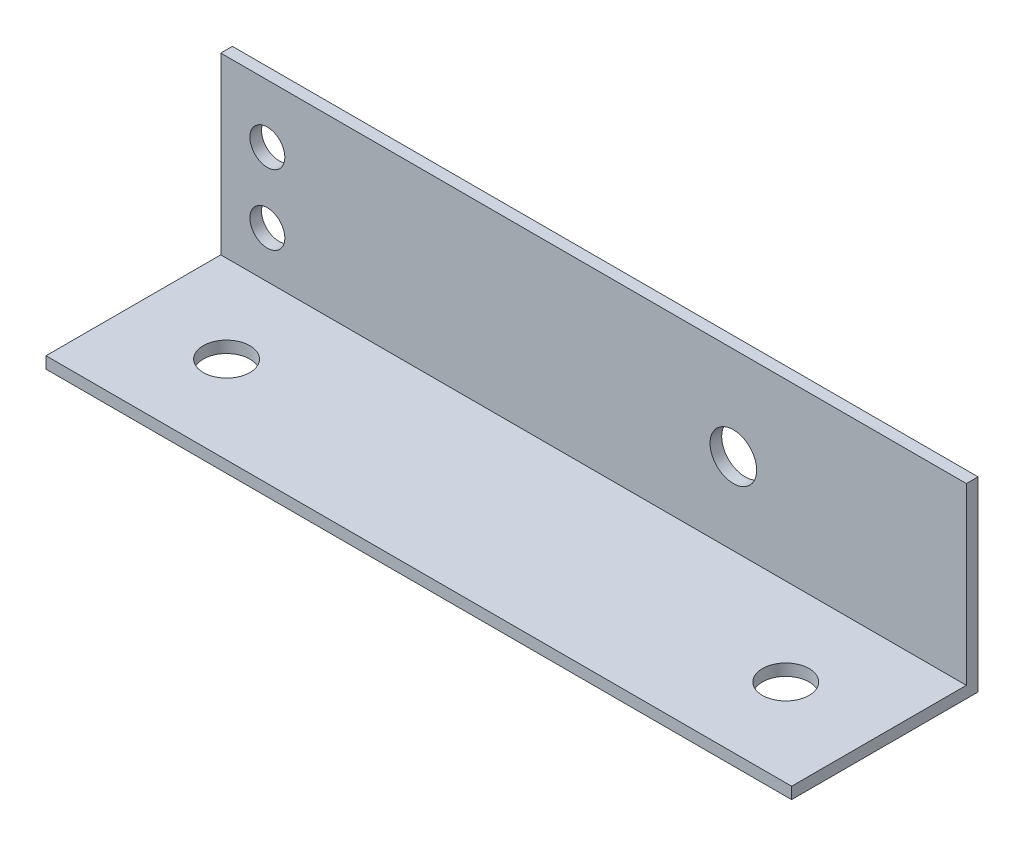
SolidWorks part; units mm, degrees
ref_plane "Front Plane" through (0, 0, 0) normal (0, 0, 1) x (1, 0, 0)
ref_plane "Top Plane" through (0, 0, 0) normal (0, 1, 0) x (1, 0, 0)
ref_plane "Right Plane" through (0, 0, 0) normal (1, 0, 0) x (0, 0, -1)
sketch "Sketch1" plane through (0, 0, 0) normal (1, 0, 0) x (0, 0, -1)
  line L0 (0, 0) -> (0, 25.4)
  line L1 (0, 25.4) -> (-1.5875, 25.4)
  line L2 (-1.5875, 25.4) -> (-1.5875, 1.5875)
  line L3 (-1.5875, 1.5875) -> (-25.4, 1.5875)
  line L4 (-25.4, 1.5875) -> (-25.4, 0)
  line L5 (-25.4, 0) -> (0, 0)
  dimension "D1" = 25.4
  dimension "D2" = 25.4
  dimension "D3" = 1.5875
  dimension "D4" = 1.5875
extrude "Boss-Extrude1" add sketch "Sketch1" along normal blind 101.6 contours L0 L1 L2 L3 L4 L5
sketch "Sketch2" plane through (0, 1.5875, 0) normal (0, 1, 0) x (1, 0, 0)
  line L0 (0, -13.4937) -> (101.6, -13.4937) construction
  line L1 (0, -1.5875) -> (0, -25.4) construction
  line L2 (101.6, -1.5875) -> (101.6, -25.4) construction
  circle A0 centre (12.7, -13.4937) radius 3.175
  circle A1 centre (88.9, -13.4937) radius 3.175
  dimension "D1" = 6.35
  dimension "D2" = 12.7
  dimension "D3" = 12.7
extrude "Cut-Extrude1" cut sketch "Sketch2" against normal blind 101.6
sketch "Sketch3" plane through (0, 0, 1.5875) normal (0, 0, 1) x (1, 0, 0)
  line L0 (0, 0) -> (0, 25.4) construction
  line L1 (0, 12.7) -> (101.6, 12.7) construction
  line L2 (101.6, 25.4) -> (101.6, 1.5875) construction
  line L3 (6.35, 7.9375) -> (6.35, 17.4625) construction
  circle A0 centre (69.85, 12.7) radius 3.175
  circle A1 centre (6.35, 17.4625) radius 2.3813
  circle A2 centre (6.35, 7.9375) radius 2.3813
  point P13 (6.35, 12.7)
  dimension "D2" = 4.7625
  dimension "D3" = 6.35
  dimension "D1" = 9.525
  dimension "D4" = 6.35
  dimension "D5" = 31.75
extrude "Cut-Extrude2" cut sketch "Sketch3" against normal blind 101.6
